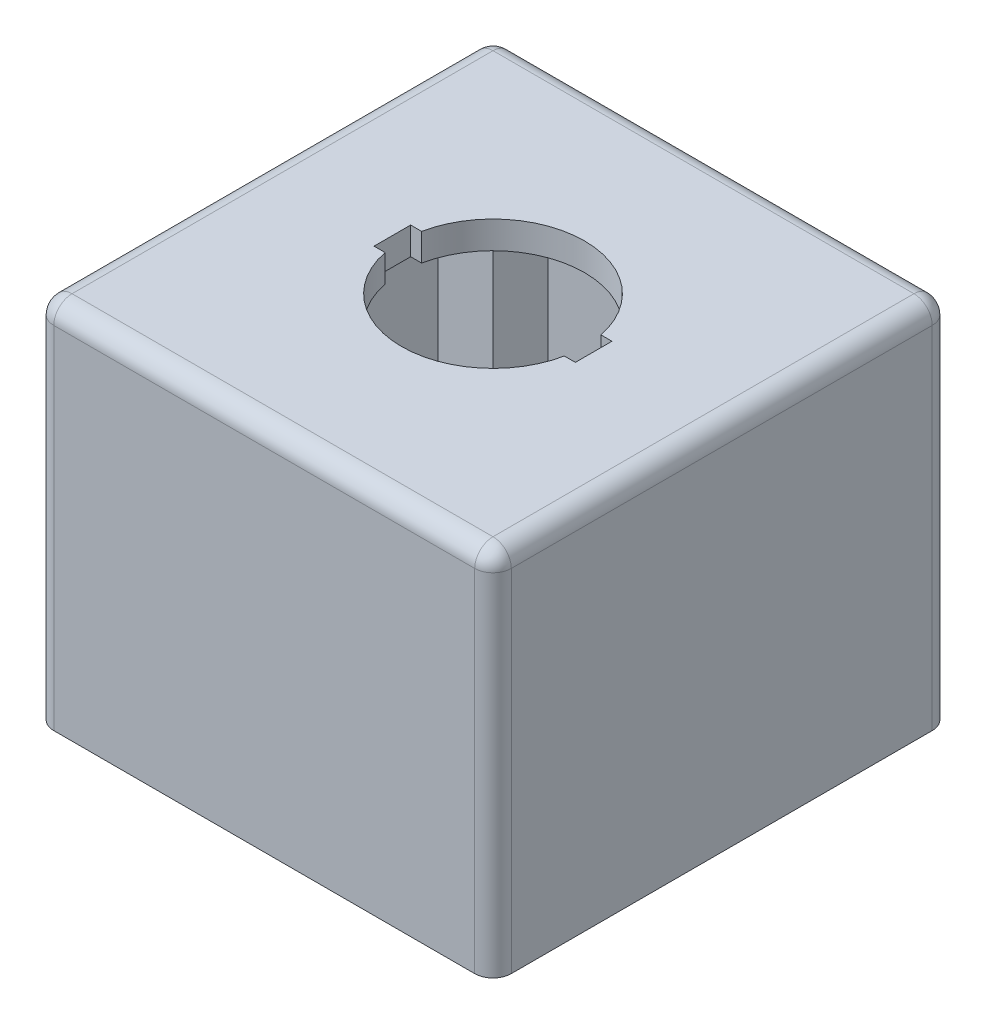
SolidWorks part; units mm, degrees
ref_plane "Front Plane" through (0, 0, 0) normal (0, 0, 1) x (1, 0, 0)
ref_plane "Top Plane" through (0, 0, 0) normal (0, 1, 0) x (1, 0, 0)
ref_plane "Right Plane" through (0, 0, 0) normal (1, 0, 0) x (0, 0, -1)
sketch "Sketch1" plane through (0, 0, 0) normal (0, 1, 0) x (1, 0, 0)
  line L1 (-25, -25) -> (25, -25)
  line L2 (-25, -25) -> (-25, 25)
  line L3 (-25, 25) -> (25, 25)
  line L4 (25, -25) -> (25, 25)
  line L5 (-25, -25) -> (25, 25) construction
  line L6 (-25, 25) -> (25, -25) construction
  point P0 (0, 0)
  dimension "D1" = 50
  dimension "D2" = 50
extrude "Boss-Extrude1" add sketch "Sketch1" along normal blind 50
shell "Shell1" thickness 3
fillet "Fillet1" radius 2 8 edges at (0, 50, 25) (-25, 50, 0) (0, 50, -25) (25, 50, 0) (25, 25, -25) (25, 25, 25) (-25, 25, -25) (-25, 25, 25)
sketch "Sketch3" plane through (0, 47, 0) normal (0, -1, 0) x (1, 0, 0)
  line L0 (0, 22) -> (0, 0) construction
  line L1 (-22, 22) -> (22, 22) construction
  line L2 (0, 0) -> (22, 0) construction
  line L3 (22, 22) -> (22, -22) construction
  line L4 (16, 22) -> (16, 16)
  line L5 (-22, 22) -> (-16, 22)
  line L6 (-22, 22) -> (-22, 16)
  line L7 (-22, 16) -> (-16, 16)
  line L8 (-16, 22) -> (-16, 16)
  line L9 (22, 16) -> (16, 16)
  line L10 (22, 22) -> (22, 16)
  line L11 (22, 22) -> (16, 22)
  line L12 (22, -22) -> (16, -22)
  line L13 (22, -22) -> (22, -16)
  line L14 (22, -16) -> (16, -16)
  line L15 (16, -22) -> (16, -16)
  line L16 (-16, -22) -> (-16, -16)
  line L17 (-22, -16) -> (-16, -16)
  line L18 (-22, -22) -> (-22, -16)
  line L19 (-22, -22) -> (-16, -22)
  dimension "D1" = 6
  dimension "D2" = 6
extrude "Boss-Extrude2" add sketch "Sketch3" along normal up to surface (47 mm away) up to face at (0, 0, 0)
sketch "Sketch4" plane through (0, 0, 0) normal (0, -1, 0) x (1, 0, 0)
  line L0 (0, 22) -> (0, 0) construction
  line L1 (-16, 22) -> (16, 22) construction
  line L2 (0, 0) -> (22, 0) construction
  line L3 (22, 16) -> (22, -16) construction
  line L4 (-16, 19) -> (-25, 19) construction
  line L5 (-16, 16) -> (-16, 22) construction
  line L6 (-25, -23) -> (-25, 23) construction
  line L8 (-22, 16) -> (-16, 16) construction
  line L9 (-19, 16) -> (-19, 19) construction
  circle A0 centre (-19, 19) radius 1.25
  circle A1 centre (19, 19) radius 1.25
  circle A2 centre (19, -19) radius 1.25
  circle A3 centre (-19, -19) radius 1.25
  dimension "D1" = 2.5
extrude "Cut-Extrude1" cut sketch "Sketch4" against normal blind 25
sketch "Sketch5" plane through (0, 50, 0) normal (0, 1, 0) x (1, 0, 0)
  line L0 (0, 23) -> (0, 0) construction
  line L1 (23, 23) -> (-23, 23) construction
  line L2 (0, 0) -> (23, 0) construction
  line L3 (23, -23) -> (23, 23) construction
  circle A0 centre (0, 0) radius 10
  dimension "D1" = 20
extrude "Cut-Extrude2" cut sketch "Sketch5" against normal through all
sketch "Sketch8" plane through (0, 50, 0) normal (0, 1, 0) x (1, 0, 0)
  line L0 (-10, 0) -> (10, 0) construction
  line L2 (-11, 2) -> (11, 2)
  line L3 (-11, 2) -> (-11, -2)
  line L4 (-11, -2) -> (11, -2)
  line L5 (11, 2) -> (11, -2)
  circle A0 centre (0, 0) radius 10 construction
  point P11 (0, 0)
  dimension "D1" = 22
  dimension "D2" = 11
  dimension "D3" = 2
  dimension "D4" = 4
extrude "Cut-Extrude4" cut sketch "Sketch8" against normal through all
sketch "Sketch9" plane through (0, 0, -25) normal (0, 0, -1) x (-1, 0, 0)
  line L0 (25, 48) -> (25, 0) construction
  line L1 (-25, 0) -> (25, 0)
  line L2 (-25, 0) -> (-25, 9.65)
  line L3 (-25, 9.65) -> (25, 9.65)
  line L4 (25, 0) -> (25, 9.65)
  line L5 (-25, 0) -> (-25, 48) construction
extrude "Cut-Extrude5" cut sketch "Sketch9" against normal through all
